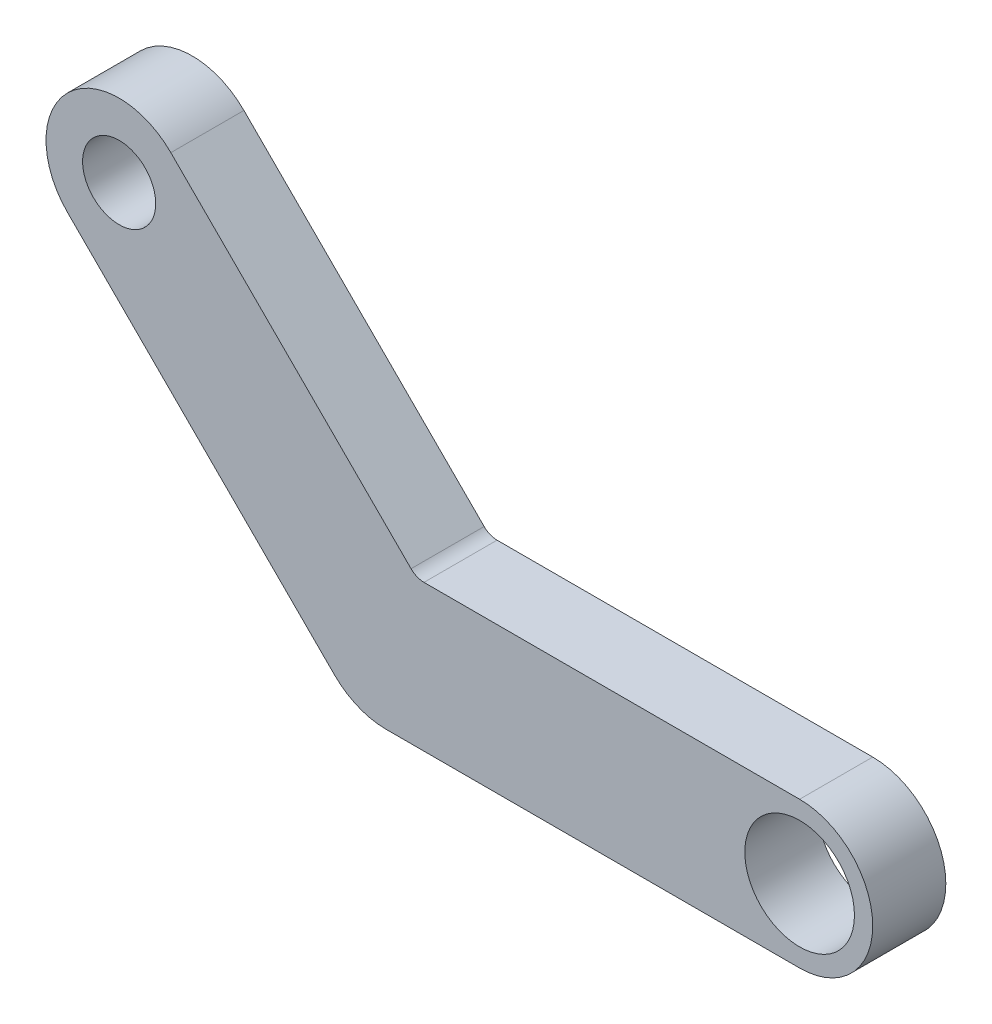
SolidWorks part; units mm, degrees
ref_plane "Front Plane" through (0, 0, 0) normal (0, 0, 1) x (1, 0, 0)
ref_plane "Top Plane" through (0, 0, 0) normal (0, 1, 0) x (1, 0, 0)
ref_plane "Right Plane" through (0, 0, 0) normal (1, 0, 0) x (0, 0, -1)
sketch "Sketch1" plane through (0, 0, 0) normal (0, 0, 1) x (1, 0, 0)
  line L0 (-3.6523, 3.6523) -> (0, 0) construction
  line L1 (-2.9452, 4.3594) -> (0.341, 1.0732)
  line L2 (-4.3594, 2.9452) -> (-0.7071, -0.7071)
  line L3 (0, 0) -> (5.6569, 0) construction
  line L4 (0.5178, 1) -> (5.6569, 1)
  line L5 (0, -1) -> (5.6569, -1)
  arc A0 (-2.9452, 4.3594) -> (-4.3594, 2.9452) centre (-3.6523, 3.6523) ccw
  arc A1 (-0.7071, -0.7071) -> (0, -1) centre (0, 0) ccw
  arc A2 (-0.7266, -0.6871) -> (0, -1) centre (0, 0) ccw
  arc A3 (5.6569, -1) -> (5.6569, 1) centre (5.6569, 0) ccw
  arc A4 (0.5178, 1) -> (0.341, 1.0732) centre (0.5178, 1.25) cw
  circle A5 centre (-3.6523, 3.6523) radius 0.5
  circle A6 centre (5.6569, 0) radius 0.75
  point P2 (-2.4291, 2.5689)
  point P7 (1.65, 0.007)
  dimension "D3" = 1
  dimension "D4" = 1
  dimension "D5" = 0.25
  dimension "D6" = 1
  dimension "D7" = 1.5
  dimension "D1" = 1
  dimension "D11" = 2
  dimension "D2" = 5.6569
  dimension "D8" = 10
  dimension "D9" = 135
  dimension "D10" = 2
extrude "Boss-Extrude1" add sketch "Sketch1" along normal blind 1 contours L4 A4 L1 A0 L2 A1 L5 A3 A6 A5
